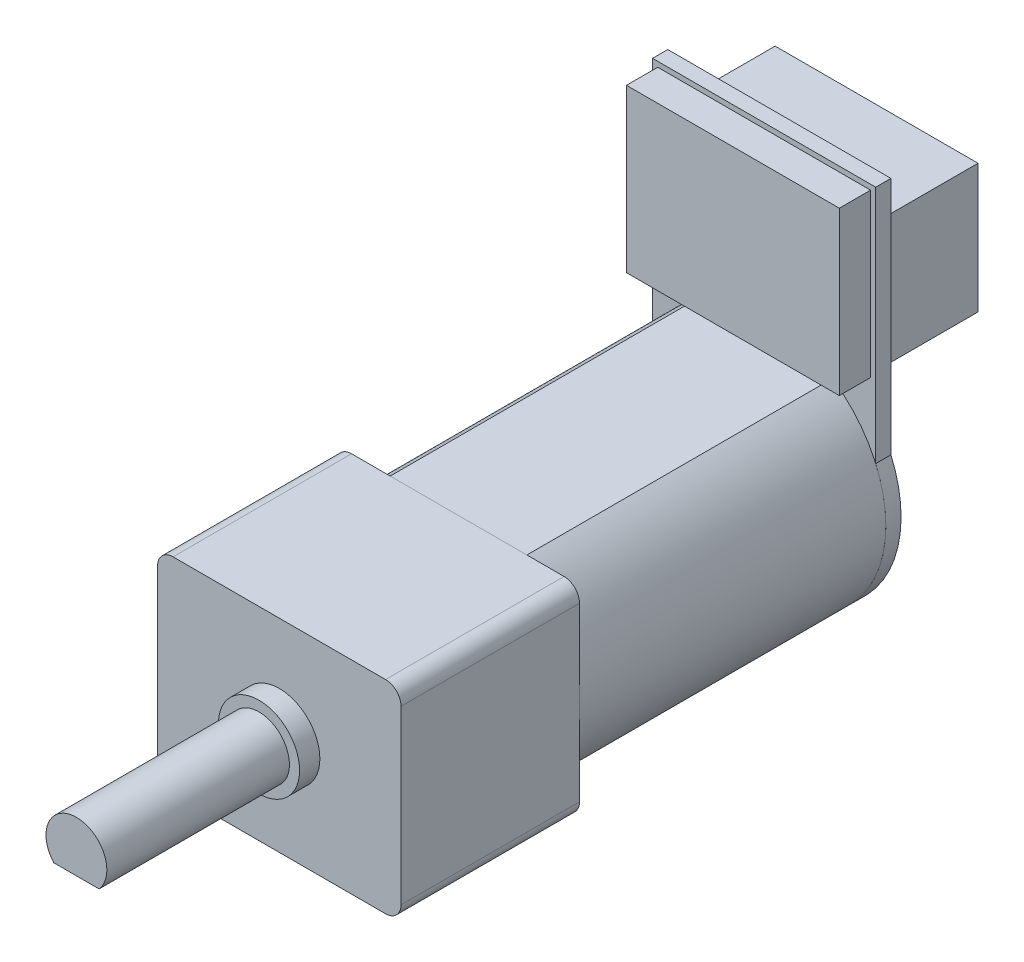
SolidWorks part; units mm, degrees
ref_plane "Front Plane" through (0, 0, 0) normal (0, 0, 1) x (1, 0, 0)
ref_plane "Top Plane" through (0, 0, 0) normal (0, 1, 0) x (1, 0, 0)
ref_plane "Right Plane" through (0, 0, 0) normal (1, 0, 0) x (0, 0, -1)
other "Bounding Box"
ref_plane "Default Plane" through (13.8565, 3.175, 6.7999) normal (0, -1, 0) x (-1, 0, 0)
sketch "Sketch1" plane through (0, 0, 0) normal (0, 0, 1) x (1, 0, 0)
  line L1 (-6, 5) -> (6, 5)
  line L2 (-6, 5) -> (-6, -5)
  line L3 (-6, -5) -> (6, -5)
  line L4 (6, 5) -> (6, -5)
  line L5 (-6, 5) -> (6, -5) construction
  line L6 (-6, -5) -> (6, 5) construction
  point P0 (0, 0)
  dimension "D1" = 12
  dimension "D2" = 10
extrude "Boss-Extrude1" add sketch "Sketch1" against normal blind 8.8
sketch "Sketch2" plane through (0, 0, 0) normal (0, 0, 1) x (1, 0, 0)
  circle A0 centre (0, 0) radius 2
  dimension "D1" = 4
extrude "Boss-Extrude2" add sketch "Sketch2" along normal blind 1
sketch "Sketch3" plane through (0, 0, 1) normal (0, 0, 1) x (1, 0, 0)
  circle A0 centre (0, 0) radius 1.5
  dimension "D1" = 3
extrude "Boss-Extrude3" add sketch "Sketch3" along normal blind 9
sketch "Sketch4" plane through (0, 0, 10) normal (0, 0, 1) x (1, 0, 0)
  line L0 (1.118, -1) -> (-1.118, -1)
  circle A0 centre (0, 0) radius 1.5 construction
  arc A1 (-1.118, -1) -> (1.118, -1) centre (0, 0) ccw
  dimension "D1" = 2.5
extrude "Cut-Extrude1" cut sketch "Sketch4" against normal blind 8
sketch "Sketch5" plane through (0, 0, -8.8) normal (0, 0, -1) x (-1, 0, 0)
  circle A0 centre (0, 0) radius 6
  dimension "D1" = 12
extrude "Boss-Extrude4" add sketch "Sketch5" along normal blind 15.1
sketch "Sketch6" plane through (0, 0, -23.9) normal (0, 0, -1) x (-1, 0, 0)
  line L0 (-3.3688, 4.965) -> (3.3688, 4.965)
  line L1 (-3.3688, -4.965) -> (3.3688, -4.965)
  line L2 (0, 4.965) -> (0, 0) construction
  line L3 (0, 0) -> (0, -4.965) construction
  circle A0 centre (0, 0) radius 6 construction
  arc A1 (-3.3688, -4.965) -> (3.3688, -4.965) centre (0, 0) ccw
  arc A2 (3.3688, 4.965) -> (-3.3688, 4.965) centre (0, 0) ccw
  dimension "D1" = 9.93
extrude "Cut-Extrude2" cut sketch "Sketch6" against normal blind 15.1
sketch "Sketch7" plane through (0, 0, -23.9) normal (0, 0, -1) x (-1, 0, 0)
  line L1 (3.3688, -4.965) -> (-3.3688, -4.965) construction
  line L3 (3.3688, -4.965) -> (-3.3688, -4.965)
  line L5 (-5.5, 14.2) -> (5.5, 14.2)
  line L6 (-5.5, 14.2) -> (-5.5, 2.3979)
  line L8 (5.5, 14.2) -> (5.5, 2.3979)
  line L9 (-5.5, 14.2) -> (5.5, 2.3979) construction
  line L10 (-5.5, 2.3979) -> (5.5, 14.2) construction
  line L11 (6, -5) -> (-6, -5) construction
  arc A0 (-3.3688, 4.965) -> (-3.3688, -4.965) centre (0, 0) ccw construction
  arc A1 (3.3688, -4.965) -> (3.3688, 4.965) centre (0, 0) ccw construction
  arc A2 (-5.5, 2.3979) -> (-3.3688, -4.965) centre (0, 0) ccw
  arc A3 (3.3688, -4.965) -> (5.5, 2.3979) centre (0, 0) ccw
  point P3 (0, 8.299)
  dimension "D1" = 11
  dimension "D2" = 19.2
extrude "Boss-Extrude5" add sketch "Sketch7" along normal blind 0.75 separate body
sketch "Sketch8" plane through (0, 0, -24.65) normal (0, 0, -1) x (-1, 0, 0)
  line L1 (-3.302, 1.143) -> (-3.048, 1.143)
  line L2 (-3.302, 1.143) -> (-3.302, -1.143)
  line L3 (-3.302, -1.143) -> (-3.048, -1.143)
  line L4 (-3.048, 1.143) -> (-3.048, -1.143)
  line L5 (-3.302, 1.143) -> (-3.048, -1.143) construction
  line L6 (-3.302, -1.143) -> (-3.048, 1.143) construction
  line L7 (3.048, 1.143) -> (3.302, 1.143)
  line L8 (3.048, 1.143) -> (3.048, -1.143)
  line L9 (3.048, -1.143) -> (3.302, -1.143)
  line L10 (3.302, 1.143) -> (3.302, -1.143)
  line L11 (3.048, 1.143) -> (3.302, -1.143) construction
  line L12 (3.048, -1.143) -> (3.302, 1.143) construction
  circle A0 centre (0, 0) radius 2
  point P3 (-3.175, 0)
  point P8 (3.175, 0)
  dimension "D1" = 4
  dimension "D2" = 3.175
  dimension "D3" = 3.175
  dimension "D4" = 2.286
  dimension "D5" = 0.254
extrude "Boss-Extrude6" add sketch "Sketch8" along normal blind 0.5
sketch "Sketch9" plane through (0, 0, -23.9) normal (0, 0, 1) x (1, 0, 0)
  line L0 (-5.5, 14.2) -> (5.5, 14.2) construction
  line L1 (-5.246, 13.946) -> (5.246, 13.946)
  line L2 (-5.246, 13.946) -> (-5.246, 5.945)
  line L3 (-5.246, 5.945) -> (5.246, 5.945)
  line L4 (5.246, 13.946) -> (5.246, 5.945)
  line L5 (-5.5, 2.3979) -> (-5.5, 14.2) construction
  line L6 (5.5, 14.2) -> (5.5, 2.3979) construction
  dimension "D1" = 0.254
  dimension "D2" = 0.254
  dimension "D3" = 0.254
  dimension "D4" = 8.001
extrude "Boss-Extrude7" add sketch "Sketch9" along normal blind 1.54
sketch "Sketch10" plane through (0, 0, -24.65) normal (0, 0, -1) x (-1, 0, 0)
  line L0 (5.5, 14.2) -> (-5.5, 14.2) construction
  line L1 (-5, 12.2) -> (5, 12.2)
  line L2 (-5, 12.2) -> (-5, 5.85)
  line L3 (-5, 5.85) -> (5, 5.85)
  line L4 (5, 12.2) -> (5, 5.85)
  line L5 (-5, 12.2) -> (5, 5.85) construction
  line L6 (-5, 5.85) -> (5, 12.2) construction
  point P0 (0, 9.025)
  dimension "D1" = 10
  dimension "D2" = 2
  dimension "D3" = 6.35
extrude "Boss-Extrude8" add sketch "Sketch10" along normal blind 4.792
fillet "Fillet1" radius 0.762 4 edges at (-6, -5, -4.4) (6, -5, -4.4) (6, 5, -4.4) (-6, 5, -4.4)
equation "\"D3@Sketch8\"=\"D2@Sketch8\""
